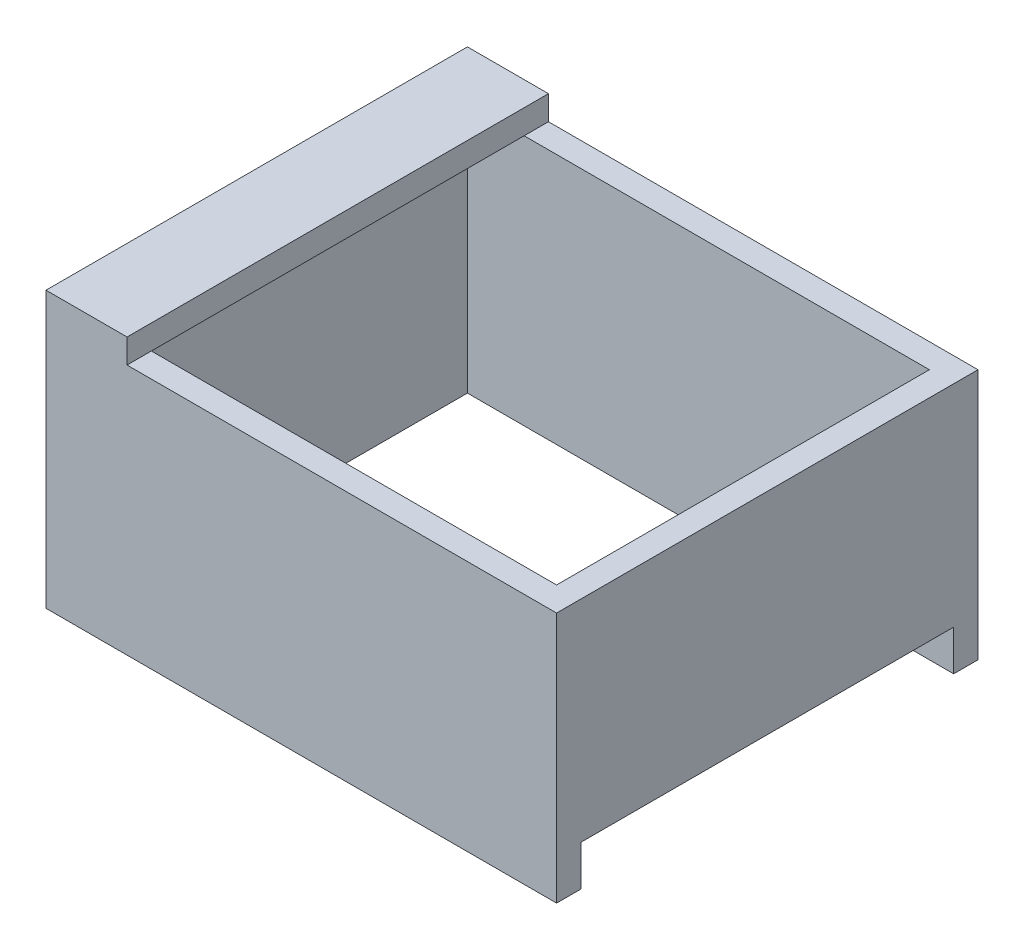
SolidWorks part; units mm, degrees
ref_plane "Front Plane" through (0, 0, 0) normal (0, 0, 1) x (1, 0, 0)
ref_plane "Top Plane" through (0, 0, 0) normal (0, 1, 0) x (1, 0, 0)
ref_plane "Right Plane" through (0, 0, 0) normal (1, 0, 0) x (0, 0, -1)
sketch "Sketch1" plane through (0, 0, 0) normal (0, 1, 0) x (1, 0, 0)
  line L1 (0, 0) -> (57, 0)
  line L2 (0, 0) -> (0, -46)
  line L3 (0, -46) -> (57, -46)
  line L4 (57, 0) -> (57, -46)
  dimension "D1" = 57
  dimension "D2" = 46
sketch "Sketch2" plane through (0, 0, 0) normal (0, 1, 0) x (1, 0, 0)
  line L8 (60, 3) -> (-3, 3)
  line L9 (60, -49) -> (60, 3)
  line L10 (-3, -49) -> (60, -49)
  line L11 (-3, 3) -> (-3, -49)
  line L12 (60, 3) -> (-3, 3)
  line L13 (60, -49) -> (60, 3)
  line L14 (-3, -49) -> (60, -49)
  line L15 (-3, 3) -> (-3, -49)
  dimension "D1" = 3
extrude "Boss-Extrude1" add sketch "Sketch2" along normal blind 31
extrude "Cut-Extrude1" cut sketch "Sketch1" along normal blind 31
sketch "Sketch3" plane through (0, 0, 0) normal (0, -1, 0) x (1, 0, 0)
  line L0 (60, 49) -> (60, -3) construction
  line L1 (57, 46) -> (60, 46)
  line L2 (57, 46) -> (57, 0)
  line L3 (57, 0) -> (60, 0)
  line L4 (60, 46) -> (60, 0)
extrude "Cut-Extrude2" cut sketch "Sketch3" against normal blind 5
sketch "Sketch4" plane through (0, 0, 46) normal (0, 0, -1) x (-1, 0, 0)
  line L1 (0, 31) -> (-57, 31) construction
  line L2 (-52, 8) -> (0, 8)
  line L3 (-52, 8) -> (-52, 11)
  line L4 (-52, 11) -> (0, 11)
  line L7 (0, 8) -> (0, 11)
  line L8 (0, 31) -> (0, 0) construction
  line L9 (-57, 31) -> (-57, 5) construction
  dimension "D1" = 20
  dimension "D2" = 3
  dimension "D3" = 0
  dimension "D4" = 5
extrude "Boss-Extrude2" add sketch "Sketch4" along normal blind 17
sketch "Sketch5" plane through (0, 31, 0) normal (0, 1, 0) x (1, 0, 0)
  line L0 (60, 3) -> (-3, 3) construction
  line L1 (-3, -49) -> (7, -49)
  line L2 (-3, -49) -> (-3, 3)
  line L3 (-3, 3) -> (7, 3)
  line L4 (7, -49) -> (7, 3)
  dimension "D1" = 10
extrude "Boss-Extrude3" add sketch "Sketch5" along normal blind 3
